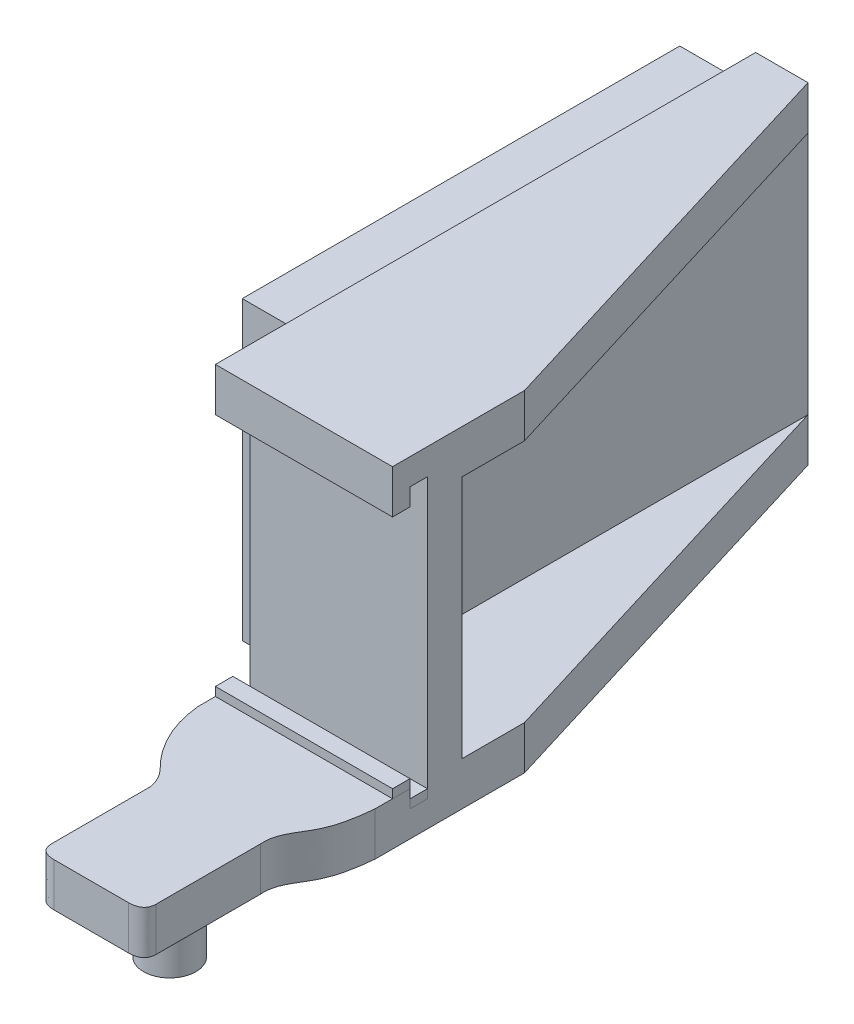
SolidWorks part; units mm, degrees
ref_plane "Alzado" through (0, 0, 0) normal (0, 0, 1) x (1, 0, 0)
ref_plane "Planta" through (0, 0, 0) normal (0, 1, 0) x (1, 0, 0)
ref_plane "Vista lateral" through (0, 0, 0) normal (1, 0, 0) x (0, 0, -1)
sketch "Croquis1" plane through (0, 0, 0) normal (0, 1, 0) x (1, 0, 0)
  line L0 (0, 30) -> (0, 0)
  line L1 (0, 0) -> (0, -2)
  line L2 (2.6172, -13.0183) -> (2.6172, -7.3446)
  line L4 (8.6172, -13.0183) -> (8.6172, -7.0183)
  line L5 (10.1631, 6.5705) -> (10.1631, 0)
  line L6 (10.1631, -2) -> (10.1631, 0)
  line L7 (10.1631, 6.5705) -> (3, 30)
  line L8 (3, 30) -> (0, 30)
  line L9 (3.4899, -13.7374) -> (7.7445, -13.7374)
  spline S0 degree 3 poles (8.6172, -7.0183) (8.5294, -6.0662) (9.8153, -4.7072) (10.0769, -2.8869) (10.1631, -2) knots 0 0 0 0 0.490317 1 1 1 1
  spline S1 degree 2 poles (0, -2) (0.2441, -4.453) (2.0609, -6.2319) knots 0 0 0 1 1 1
  spline S2 degree 2 poles (2.0609, -6.2319) (2.507, -6.7126) (2.6172, -7.3446) knots 0 0 0 1 1 1
  spline S3 degree 2 poles (2.6172, -13.0183) (2.6309, -13.735) (3.4899, -13.7374) knots 0 0 0 1 1 1
  spline S4 degree 2 poles (8.6172, -13.0183) (8.6035, -13.735) (7.7445, -13.7374) knots 0 0 0 1 1 1
  dimension "D1" = 3
  dimension "D2" = 30
  dimension "D3" = 24.5
  dimension "D4" = 6
  dimension "D6" = 2
  dimension "D7" = 6
extrude "Saliente-Extruir1" add sketch "Croquis1" along normal blind 19
sketch "Croquis2" plane through (0, 0, -30) normal (0, 0, -1) x (-1, 0, 0)
  line L0 (-3, 19) -> (-3, 16.5)
  line L1 (-3, 19) -> (-3, 0) construction
  line L2 (-3, 16.5) -> (-12.8726, 16.5)
  line L3 (-12.8726, 16.5) -> (-12.8726, 2.5)
  line L4 (-12.8726, 2.5) -> (-3, 2.5)
  line L5 (-3, 2.5) -> (-3, 16.5)
  line M6 (-3, 19) -> (-3, 0)
  dimension "D1" = 2.5
  dimension "D2" = 2.5
extrude "Cortar-Extruir1" cut sketch "Croquis2" against normal blind 27 contours L3 L4 L2 M6
sketch "Croquis10" plane through (0, 0, 0) normal (1, 0, 0) x (0, 0, -1)
  line L0 (1, 2.5) -> (1, 16.5)
  line L1 (1, 2.5) -> (-1, 2.5)
  line L2 (1, 16.5) -> (-1, 16.5)
  line L3 (-1, 2.5) -> (-13.7374, 2.5)
  line L4 (-1, 19) -> (-13.7374, 19)
  line L5 (-13.7374, 19) -> (-13.7374, 0) construction
  line L8 (-13.7374, 2.5) -> (-13.7374, 19)
  line L10 (-1, 16.5) -> (-1, 19)
  line L11 (1, 16.5) -> (-1, 16.5)
  dimension "D1" = 2
sketch "Croquis13" plane through (0, 0, 0) normal (-1, 0, 0) x (0, 0, 1)
  line L0 (-29.1429, 18) -> (-4.0429, 18)
  line L1 (-4.0429, 18) -> (-4.0429, 1)
  line L2 (-4.0429, 1) -> (-29.1429, 1)
  line L4 (-30, 19) -> (2, 19) construction
  line L5 (-29.1429, 1) -> (-29.1429, 18)
  line L6 (-30, 0) -> (1, 0) construction
  dimension "D1" = 1
  dimension "D2" = 1
  dimension "D3" = 25.1
extrude "Saliente-Extruir5" add sketch "Croquis13" along normal blind 3.5
extrude "Cortar-Extruir3" cut sketch "Croquis10" along normal blind 23 contours L2 L10 L4 L8 L3 L1 L0
sketch "Croquis14" plane through (0, 0, 0) normal (-1, 0, 0) x (0, 0, 1)
  line L0 (-1, 16.5) -> (-1, 17.5)
  line L1 (-1, 17.5) -> (0, 17.5)
  line L2 (0, 17.5) -> (0, 16.5)
  line L3 (-1, 16.5) -> (1, 16.5) construction
  line L4 (0, 16.5) -> (-1, 16.5)
  line L8 (0, 2.5) -> (-1, 2.5)
  line L9 (0, 1.5) -> (0, 2.5)
  line L10 (-1, 1.5) -> (0, 1.5)
  line L11 (-1, 2.5) -> (-1, 1.5)
  dimension "D1" = 1
extrude "Cortar-Extruir4" cut sketch "Croquis14" against normal blind 23
sketch "Croquis15" plane through (0, 0, 0) normal (0, -1, 0) x (1, 0, 0)
  line L0 (3.4899, 13.7374) -> (7.7445, 13.7374) construction
  circle A0 centre (5.6172, 9.2374) radius 1.5
  dimension "D1" = 3
extrude "Saliente-Extruir6" add sketch "Croquis15" along normal blind 3.5
sketch "Croquis16" plane through (0, 0, 0) normal (-1, 0, 0) x (0, 0, 1)
  line L0 (0, 1.5) -> (0, 2)
  line L1 (0, 1.5) -> (0, 2.5) construction
  line L2 (0, 2) -> (-1, 2)
  line L3 (-1, 1.5) -> (-1, 17.5) construction
  line L4 (-1, 2) -> (-1, 1.5)
  line L5 (-1, 1.5) -> (0, 1.5)
  line L6 (0, 2.5) -> (0, 3)
  line L7 (0, 3) -> (1, 3)
  line L8 (1, 3) -> (1, 2.5)
  line L9 (0, 2.5) -> (2, 2.5) construction
  line L10 (1, 2.5) -> (0, 2.5)
  dimension "D1" = 0.5
  dimension "D2" = 1
extrude "Saliente-Extruir7" add sketch "Croquis16" against normal blind 10.165
